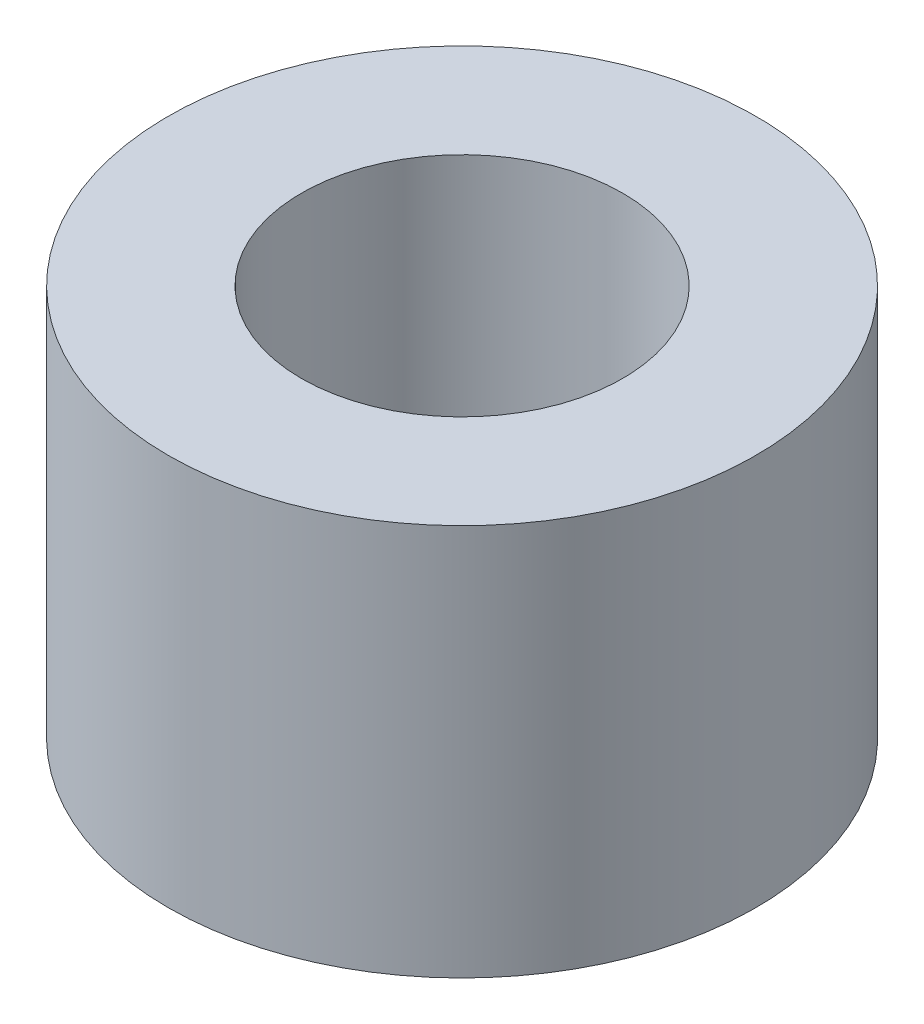
SolidWorks part; units mm, degrees
ref_plane "Front Plane" through (0, 0, 0) normal (0, 0, 1) x (1, 0, 0)
ref_plane "Top Plane" through (0, 0, 0) normal (0, 1, 0) x (1, 0, 0)
ref_plane "Right Plane" through (0, 0, 0) normal (1, 0, 0) x (0, 0, -1)
sketch "Sketch1" plane through (0, 0, 0) normal (0, 1, 0) x (1, 0, 0)
  circle A0 centre (0, 0) radius 4.1
  circle A1 centre (0, 0) radius 7.5
  dimension "D1" = 8.2
  dimension "D2" = 15
extrude "Boss-Extrude1" add sketch "Sketch1" along normal blind 10
